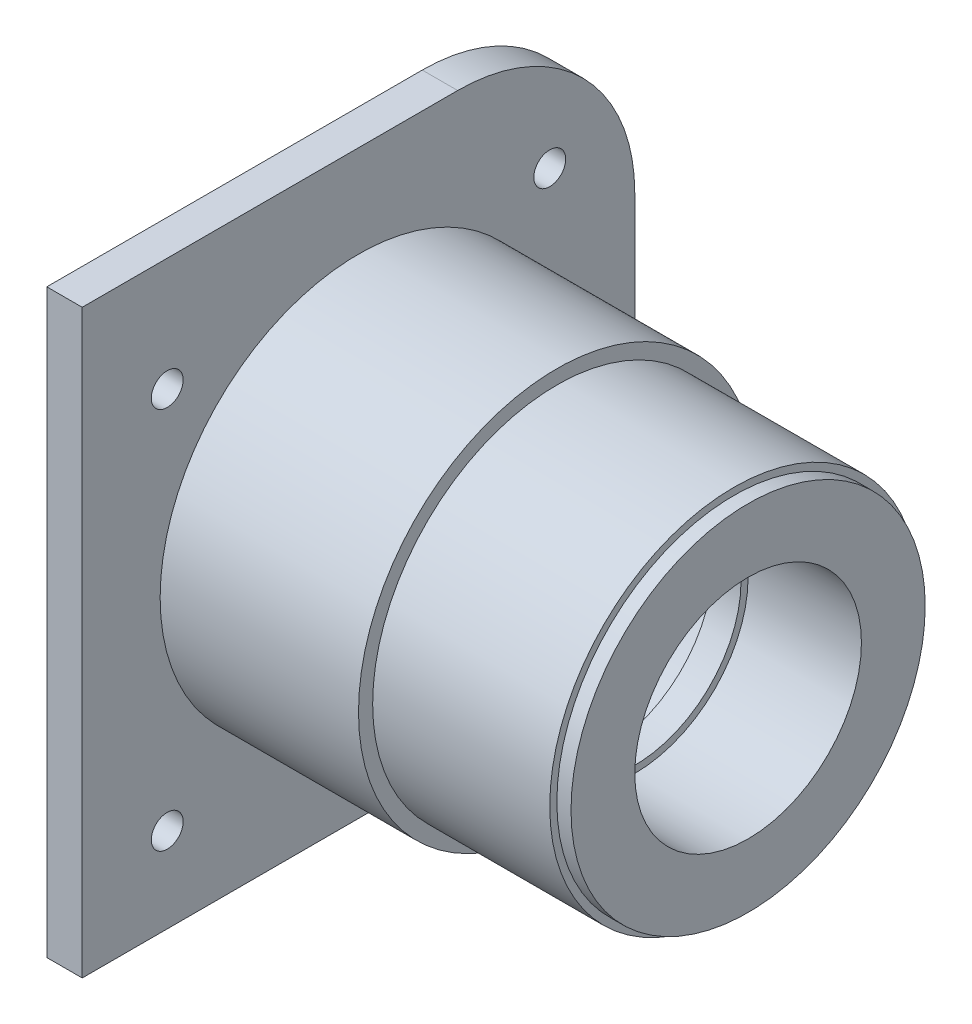
SolidWorks part; units mm, degrees
material "1060 Alloy"
ref_plane "Front Plane" through (0, 0, 0) normal (0, 0, 1) x (1, 0, 0)
ref_plane "Top Plane" through (0, 0, 0) normal (0, 1, 0) x (1, 0, 0)
ref_plane "Right Plane" through (0, 0, 0) normal (1, 0, 0) x (0, 0, -1)
sketch "Sketch2" plane through (0, 0, 0) normal (0, 0, 1) x (1, 0, 0)
  line L0 (-64.1034, 0) -> (113.4236, 0) construction
  line L2 (0, 21) -> (35, 21)
  line L3 (0, -55) -> (0, 55) construction
  line L13 (35, 21) -> (35, 15)
  line L14 (35, 15) -> (39, 15)
  line L15 (39, 15) -> (39, 16)
  line L16 (39, 16) -> (55, 16)
  line L17 (55, 16) -> (55, 26)
  line L18 (55, 26) -> (28, 26)
  line L19 (28, 26) -> (28, 28)
  line L20 (28, 28) -> (0, 28)
  line L21 (0, 28) -> (0, 21)
  point P14 (37, 15)
  dimension "D1" = 21
  dimension "D2" = 35
  dimension "D3" = 15
  dimension "D4" = 4
  dimension "D5" = 16
  dimension "D6" = 26
  dimension "D7" = 16
  dimension "D8" = 28
  dimension "D9" = 28
revolve "Revolve1" add sketch "Sketch2" angle 360 about L0
ref_plane "Plane1" through (53, 0, 0) normal (1, 0, 0) x (0, 0, -1)
sketch "Sketch3" plane through (53, 0, 0) normal (1, 0, 0) x (0, 0, -1)
  circle A0 centre (0, 0) radius 25
  circle A1 centre (0, 0) radius 26 construction
  circle A2 centre (0, 0) radius 27.5
  dimension "D1" = 1
  dimension "D2" = 55
extrude "Cut-Extrude1" cut sketch "Sketch3" along normal blind 2
sketch "Sketch4" plane through (0, 0, 0) normal (-1, 0, 0) x (0, 0, 1)
  line L14 (-21, -21) -> (21, -21)
  line L15 (-21, -21) -> (-21, 21)
  line L16 (-39, -41) -> (39, -41)
  line L17 (-39, -41) -> (-39, 41)
  line L18 (-39, 41) -> (39, 41)
  line L19 (39, -41) -> (39, 41)
  line L20 (-39, -41) -> (39, 41) construction
  line L21 (-39, 41) -> (39, -41) construction
  line L22 (-21, 21) -> (21, 21)
  line L23 (21, -21) -> (21, 21)
  line L24 (-21, -21) -> (21, 21) construction
  line L25 (-21, 21) -> (21, -21) construction
  circle A2 centre (0, 0) radius 21 construction
  point P0 (0, 0)
  point P1 (0, 0)
  point P2 (0, 0)
  point P6 (0, 0)
  point P9 (0, 21)
  point P10 (0, 0)
  point P18 (21, 0)
  dimension "D1" = 82
  dimension "D2" = 78
extrude "Boss-Extrude1" add sketch "Sketch4" along normal blind 5
hole_wizard "M4 Clearance Hole1" positions "Sketch9" profile "Sketch10" hole size "M4" standard "ANSI Metric" end condition up to next
sketch "Sketch9" plane through (-5, 0, 0) normal (-1, 0, 0) x (0, 0, 1)
  line L0 (39, 41) -> (-39, 41) construction
  line L1 (39, -41) -> (39, 41) construction
  line L2 (-39, 41) -> (-39, -41) construction
  point P0 (-27, 25)
  point P2 (27, 25)
  point P4 (27, -29)
  point P6 (-27, -29)
  dimension "D1" = 16
  dimension "D2" = 12
  dimension "D3" = 12
  dimension "D4" = 54
sketch "Sketch10" plane through (-5, 25, -27) normal (0, 1, 0) x (0, 0, 1)
  line L0 (0, 0) -> (0, 5)
  line L1 (0, 5) -> (2.25, 5)
  line L2 (2.25, 5) -> (2.25, 0)
  line L5 (2.25, 0) -> (0, 0)
  line L11 (0, -6.35) -> (0, 107.95) construction
  dimension "Thru Hole Dia." = 4.5
  dimension "Thru Hole Depth" = 5
sketch "Sketch11" plane through (0, 0, 0) normal (-1, 0, 0) x (0, 0, 1)
  line L0 (-21, 18) -> (-18, 21)
  line L1 (-21, 21) -> (-21, -21) construction
  line L2 (0, 21) -> (-18.5203, 21) construction
  line L3 (-18, 21) -> (-21, 21)
  line L4 (-21, 21) -> (-21, 18)
  line L5 (21, 21) -> (21, 18)
  line L6 (21, 0) -> (21, 18.5203) construction
  line L7 (21, 18) -> (18, 21)
  line L8 (18.5203, 21) -> (0, 21) construction
  line L9 (18, 21) -> (21, 21)
  line L10 (21, -21) -> (21, -18)
  line L11 (21, -21) -> (21, 21) construction
  line L12 (21, -18) -> (18, -21)
  line L13 (0, -21) -> (18.5203, -21) construction
  line L14 (18, -21) -> (21, -21)
  line L15 (-21, -21) -> (-21, -18)
  line L16 (-21, 0) -> (-21, -18.5203) construction
  line L17 (-21, -18) -> (-18, -21)
  line L18 (-18.5203, -21) -> (0, -21) construction
  line L19 (-18, -21) -> (-21, -21)
  dimension "D1" = 3
  dimension "D2" = 3
  dimension "D3" = 3
  dimension "D4" = 3
  dimension "D5" = 3
extrude "Boss-Extrude4" add sketch "Sketch11" along normal blind 5
fillet "Fillet1" radius 25 2 edges at (-2.5, -41, -39) (-2.5, 41, -39)
